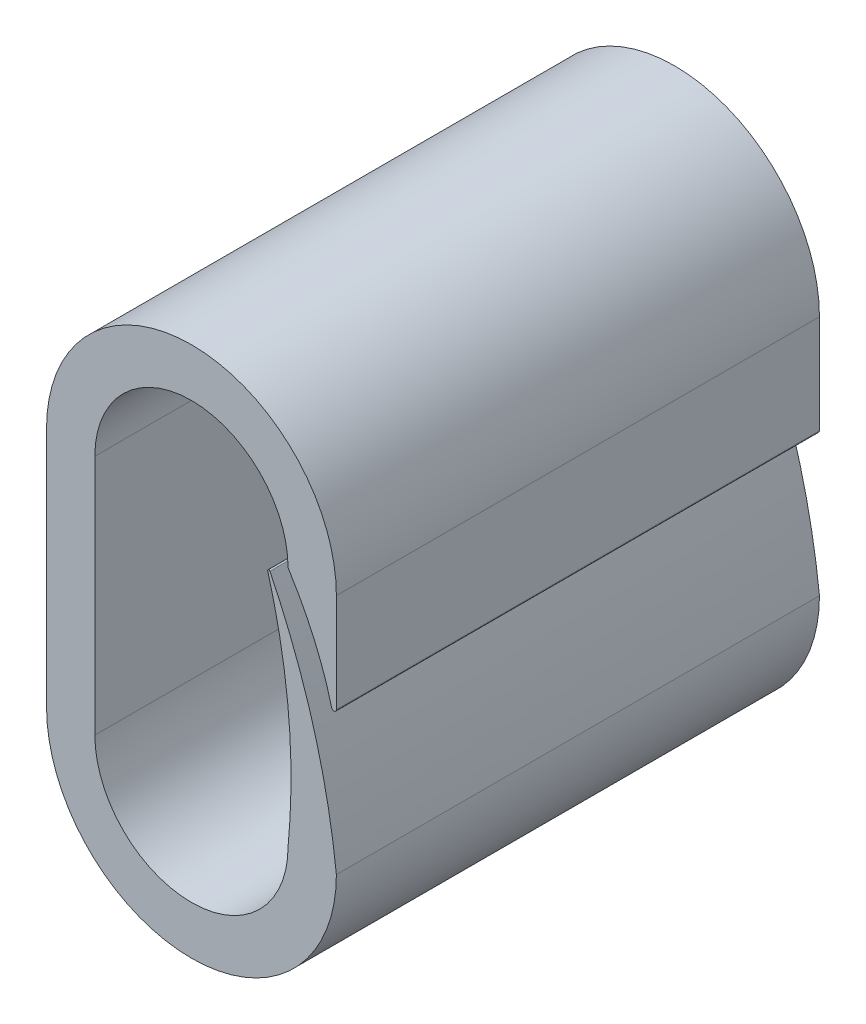
SolidWorks part; units mm, degrees
ref_plane "Front Plane" through (0, 0, 0) normal (0, 0, 1) x (1, 0, 0)
ref_plane "Top Plane" through (0, 0, 0) normal (0, 1, 0) x (1, 0, 0)
ref_plane "Right Plane" through (0, 0, 0) normal (1, 0, 0) x (0, 0, -1)
sketch "Sketch1" plane through (0, 0, 0) normal (0, 0, 1) x (1, 0, 0)
  line L0 (0, -2.5) -> (0, 2.5) construction
  line L1 (-2, -2.5) -> (-2, 2.5)
  line L2 (2, -2.5) -> (2, 2.5)
  line L3 (-3, -2.5) -> (-3, 2.5)
  line L4 (3, -2.5) -> (3, 2.5)
  line L6 (2, 2.5) -> (3, 2.5)
  line L7 (2, 2.5) -> (2, -2.5)
  line L8 (2, -2.5) -> (3, -2.5)
  line L9 (3, 2.5) -> (3, -2.5)
  line L10 (2, 2.5) -> (3, -2.5) construction
  line L11 (2, -2.5) -> (3, 2.5) construction
  line L12 (-1.5, -2.5) -> (-1.5, 2.5) construction
  line L13 (1.5, -2.5) -> (1.5, 2.5) construction
  arc A0 (-2, -2.5) -> (2, -2.5) centre (0, -2.5) ccw
  arc A1 (2, 2.5) -> (-2, 2.5) centre (0, 2.5) ccw
  arc A2 (3, 2.5) -> (-3, 2.5) centre (0, 2.5) ccw
  arc A3 (-3, -2.5) -> (3, -2.5) centre (0, -2.5) ccw
  arc A4 (1.5, 2.5) -> (-1.5, 2.5) centre (0, 2.5) ccw construction
  arc A5 (-1.5, -2.5) -> (1.5, -2.5) centre (0, -2.5) ccw construction
  spline S0 degree 2 poles (3, -2.5) (2.7094, 0.1366) (1.5, 2.5) knots 0 0 0 1 1 1
  spline S1 degree 2 poles (2, -2.5) (2.2451, 0.049) (1.5, 2.5) knots 0 0 0 1 1 1
  spline S2 degree 2 poles (2, 2.5) (3.4642, 0.1857) (3, -2.5) knots 0 0 0 1 1 1
  point P2 (0, 0)
  point P14 (2.5, 0)
  point P19 (2, 0)
  point P20 (3, 0)
  point P21 (2.5, 2.5)
  dimension "D1" = 5
  dimension "D2" = 4
  dimension "D4" = 0
  dimension "D5" = 0
  dimension "D6" = 0
  dimension "D7" = 5
  dimension "D3" = 1
  dimension "D9" = 0.5
extrude "Boss-Extrude1" add sketch "Sketch1" along normal blind 10
ref_plane "mid_x" through (0, 0, 5) normal (0, 0, 1) x (1, 0, 0)
fillet "Fillet1" radius 0.025 1 edges at (1.5, 2.5, 5)
fillet "Fillet2" radius 0.05 1 edges at (3, 0, 5)
